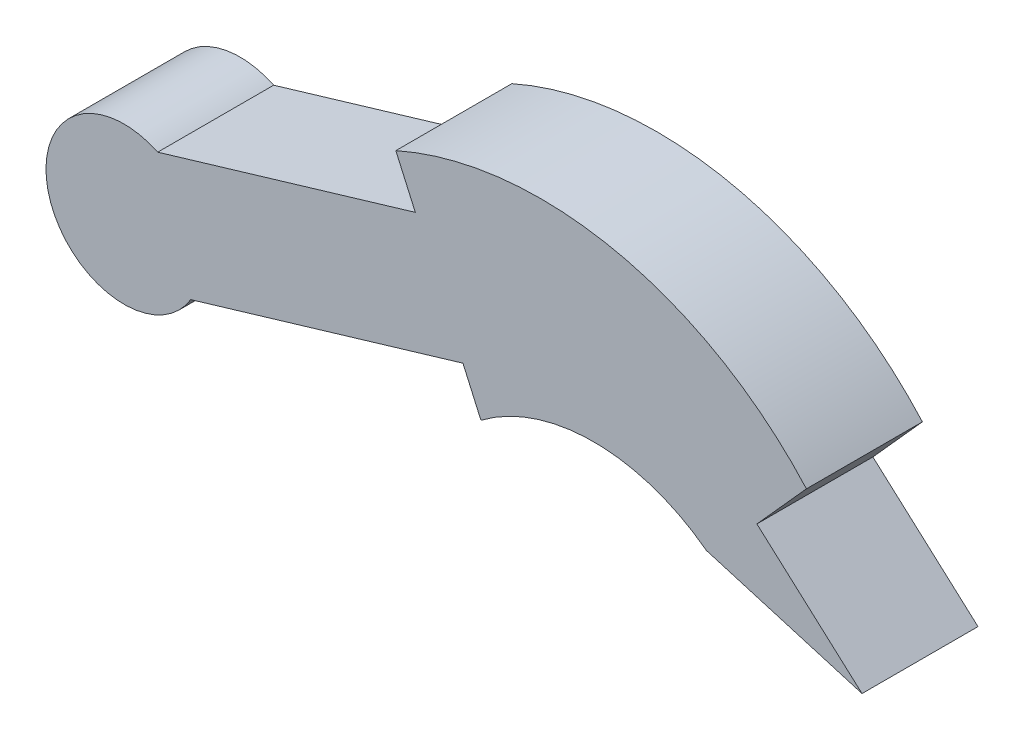
SolidWorks part; units mm, degrees
ref_plane "Front Plane" through (0, 0, 0) normal (0, 0, 1) x (1, 0, 0)
ref_plane "Top Plane" through (0, 0, 0) normal (0, 1, 0) x (1, 0, 0)
ref_plane "Right Plane" through (0, 0, 0) normal (1, 0, 0) x (0, 0, -1)
sketch "Sketch1" plane through (0, 0, 0) normal (0, 0, 1) x (1, 0, 0)
  line L0 (25.0182, 1.4583) -> (28.403, 2.4658)
  line L1 (28.403, 2.4658) -> (28.1471, 3.0402)
  line L2 (29.2652, 0.531) -> (29.0286, 1.062)
  line L3 (29.0286, 1.062) -> (25.453, -0.0024)
  line L4 (33.5417, 1.8892) -> (32.891, 1.1643)
  line L5 (32.891, 1.1643) -> (34.272, -0.0753)
  line L6 (34.272, -0.0753) -> (32.2265, 0.531)
  arc A0 (25.453, -0.0024) -> (25.0182, 1.4583) centre (24.5767, 0.5318) cw
  arc A1 (29.2652, 0.531) -> (32.2265, 0.531) centre (30.7458, -1.4303) cw
  arc A2 (28.1471, 3.0402) -> (33.5417, 1.8892) centre (30.0548, -1.2361) cw
extrude "Boss-Extrude1" add sketch "Sketch1" against normal blind 1.524
